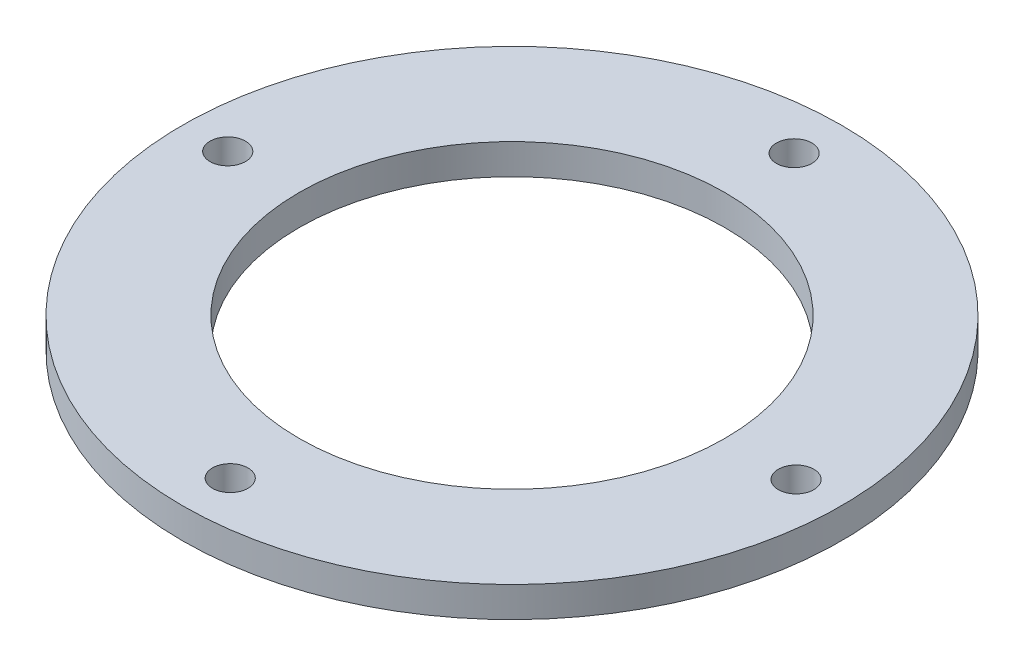
SolidWorks part; units mm, degrees
ref_plane "Front Plane" through (0, 0, 0) normal (0, 0, 1) x (1, 0, 0)
ref_plane "Top Plane" through (0, 0, 0) normal (0, 1, 0) x (1, 0, 0)
ref_plane "Right Plane" through (0, 0, 0) normal (1, 0, 0) x (0, 0, -1)
sketch "Sketch1" plane through (0, 0, 0) normal (0, 1, 0) x (1, 0, 0)
  circle A0 centre (0, 0) radius 32.5
  circle A1 centre (0, 0) radius 21
  dimension "D1" = 65
  dimension "D2" = 42
extrude "Boss-Extrude2" add sketch "Sketch1" along normal blind 3
sketch "Sketch2" plane through (0, 3, 0) normal (0, 1, 0) x (1, 0, 0)
  circle A0 centre (0, -27.7889) radius 1.75
  dimension "D1" = 3.5
extrude "Cut-Extrude2" cut sketch "Sketch2" against normal through all both and the other way through all
sketch "Sketch5" plane through (0, 3, 0) normal (0, 1, 0) x (1, 0, 0)
  line L0 (0, 32.5) -> (0, 29.79)
  circle A0 centre (0.0578, 27.7663) radius 1.75
  circle A1 centre (0, 0) radius 32.5 construction
  dimension "D1" = 3.5
  dimension "D2" = 2.71
extrude "Cut-Extrude4" cut sketch "Sketch5" against normal through all both and the other way through all contours A0
sketch "Sketch13" plane through (0, 3, 0) normal (0, 1, 0) x (1, 0, 0)
  line L0 (-32.5, 0) -> (-29.79, 0)
  line L1 (32.5, 0) -> (29.79, 0)
  circle A0 centre (0, 0) radius 32.5 construction
  circle A1 centre (-28.0274, -0.004) radius 1.75
  circle A2 centre (28.0162, 0) radius 1.75
  dimension "D3" = 3.5
  dimension "D4" = 3.5
  dimension "D1" = 2.71
  dimension "D2" = 2.71
extrude "Cut-Extrude12" cut sketch "Sketch13" against normal through all both and the other way through all contours A1 | A2
